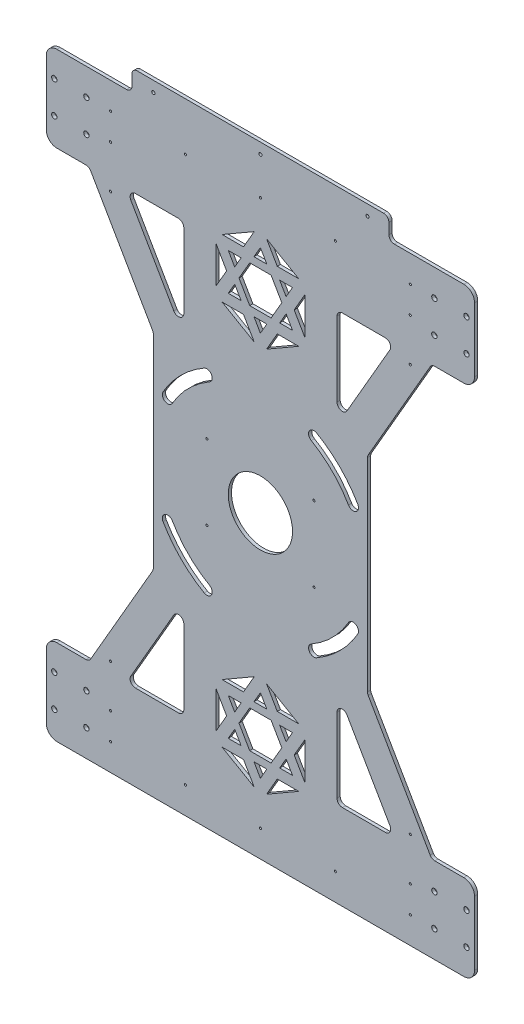
SolidWorks part; units mm, degrees
material "A-玻璃纤维"
ref_plane "前视基准面" through (0, 0, 0) normal (0, 0, 1) x (1, 0, 0)
ref_plane "上视基准面" through (0, 0, 0) normal (0, 1, 0) x (1, 0, 0)
ref_plane "右视基准面" through (0, 0, 0) normal (1, 0, 0) x (0, 0, -1)
other "Configuration Table"
sketch "草图2" plane through (0, 0, 0) normal (0, 0, 1) x (1, 0, 0)
  line L0 (-286.4774, 0) -> (382.3503, 0) construction
  line L1 (0, 257.3731) -> (0, 0) construction
  line L2 (-190, 280) -> (-125, 280)
  line L3 (200, 270) -> (200, 210)
  line L4 (190, 200) -> (162.8868, 200)
  line L5 (100, 94.7372) -> (100, -94.7372)
  line L6 (-100, 94.7372) -> (-100, -94.7372)
  line L7 (-190, 200) -> (-162.8868, 200)
  line L8 (-200, 270) -> (-200, 210)
  line L9 (-200, -270) -> (-200, -210)
  line L10 (-190, -200) -> (-162.8868, -200)
  line L11 (190, -200) -> (162.8868, -200)
  line L12 (200, -270) -> (200, -210)
  line L13 (-190, -280) -> (190, -280)
  line L14 (-120, 285) -> (-120, 295)
  line L15 (-115, 300) -> (115, 300)
  line L16 (120, 285) -> (120, 295)
  line L17 (125, 280) -> (190, 280)
  line L18 (100.6699, 97.2372) -> (158.5566, 197.5)
  line L19 (100.6699, -97.2372) -> (158.5566, -197.5)
  line L20 (-100.6699, -97.2372) -> (-158.5566, -197.5)
  line L21 (-100.6699, 97.2372) -> (-158.5566, 197.5)
  line L22 (0, -280) -> (0, -355.5287) construction
  arc A1 (200, 210) -> (190, 200) centre (190, 210) cw
  arc A2 (190, 280) -> (200, 270) centre (190, 270) cw
  arc A3 (-190, 280) -> (-200, 270) centre (-190, 270) ccw
  arc A4 (-200, 210) -> (-190, 200) centre (-190, 210) ccw
  arc A7 (-200, -210) -> (-190, -200) centre (-190, -210) cw
  arc A8 (-190, -280) -> (-200, -270) centre (-190, -270) cw
  arc A9 (190, -280) -> (200, -270) centre (190, -270) ccw
  arc A10 (200, -210) -> (190, -200) centre (190, -210) ccw
  arc A12 (120, 295) -> (115, 300) centre (115, 295) ccw
  arc A13 (-120, 295) -> (-115, 300) centre (-115, 295) cw
  arc A14 (120, 285) -> (125, 280) centre (125, 285) ccw
  arc A15 (-120, 285) -> (-125, 280) centre (-125, 285) cw
  arc A16 (158.5566, -197.5) -> (162.8868, -200) centre (162.8868, -195) ccw
  arc A17 (158.5566, 197.5) -> (162.8868, 200) centre (162.8868, 195) cw
  arc A18 (100.6699, 97.2372) -> (100, 94.7372) centre (105, 94.7372) ccw
  arc A19 (100.6699, -97.2372) -> (100, -94.7372) centre (105, -94.7372) cw
  arc A20 (-158.5566, -197.5) -> (-162.8868, -200) centre (-162.8868, -195) cw
  arc A21 (-100.6699, -97.2372) -> (-100, -94.7372) centre (-105, -94.7372) ccw
  arc A22 (-100.6699, 97.2372) -> (-100, 94.7372) centre (-105, 94.7372) cw
  arc A23 (-158.5566, 197.5) -> (-162.8868, 200) centre (-162.8868, 195) ccw
  point P5 (-200, 280)
  point P10 (-100, -200)
  point P12 (100, 200)
  point P15 (200, 200)
  point P18 (200, 280)
  point P26 (120, 280)
  point P28 (100, 0)
  point P29 (0, 280)
  point P30 (-200, 200)
  point P31 (-100, 200)
  point P47 (-120, 280)
  point P50 (-100, 0)
  point P51 (-200, -200)
  point P52 (0, -280)
  point P53 (200, -280)
  point P54 (200, -200)
  point P55 (100, -200)
  point P56 (-200, -280)
  point P61 (0, 300)
  point P64 (120, 300)
  point P67 (-120, 300)
  point P70 (160, -200)
  point P77 (160, 200)
  point P80 (100, 96.077)
  point P83 (100, -96.077)
  point P86 (-160, -200)
  point P89 (-100, -96.077)
  point P92 (-100, 96.077)
  point P95 (-160, 200)
  dimension "D5" = 5
  dimension "D8" = 5
  dimension "D11" = 5
  dimension "D1" = 400
  dimension "D2" = 80
  dimension "D3" = 100
  dimension "D4" = 560
  dimension "D6" = 120
  dimension "D7" = 20
  dimension "D9" = 30
  dimension "D10" = 120
extrude "凸台-拉伸1" add sketch "草图2" along normal blind 3
sketch "草图3" plane through (0, 0, 3) normal (0, 0, 1) x (1, 0, 0)
  line L0 (-216.9525, -240) -> (342.3439, -240) construction
  line L1 (-162.5, -255) -> (-162.5, -225) construction
  line L2 (-162.5, -225) -> (-192.5, -225) construction
  line L3 (-192.5, -225) -> (-192.5, -255) construction
  line L4 (-192.5, -255) -> (-162.5, -255) construction
  line L6 (-200, -210) -> (-200, -270) construction
  line L7 (-228.6627, 0) -> (0, 0) construction
  line L8 (0, 0) -> (0, 177.0482) construction
  circle A0 centre (-177.5, -240) radius 15 construction
  circle A1 centre (-162.5, -225) radius 2.5
  circle A2 centre (-192.5, -225) radius 2.5
  circle A3 centre (-192.5, -255) radius 2.5
  circle A4 centre (-162.5, -255) radius 2.5
  circle A5 centre (-162.5, 255) radius 2.5
  circle A6 centre (-192.5, 255) radius 2.5
  circle A7 centre (-192.5, 225) radius 2.5
  circle A8 centre (-162.5, 225) radius 2.5
  circle A9 centre (192.5, -255) radius 2.5
  circle A10 centre (192.5, -225) radius 2.5
  circle A11 centre (162.5, -225) radius 2.5
  circle A12 centre (162.5, -255) radius 2.5
  circle A13 centre (162.5, 225) radius 2.5
  circle A14 centre (192.5, 225) radius 2.5
  circle A15 centre (192.5, 255) radius 2.5
  circle A16 centre (162.5, 255) radius 2.5
  dimension "D3" = 5
  dimension "D1" = 30
  dimension "D2" = 7.5
extrude "切除-拉伸1" cut sketch "草图3" against normal blind 3
sketch "草图5" plane through (0, 0, 3) normal (0, 0, 1) x (1, 0, 0)
  line L0 (-120, 295) -> (-120, 285) construction
  line L1 (115, 300) -> (-115, 300) construction
  line L2 (120, 285) -> (120, 295) construction
  circle A0 centre (0, 290) radius 1.5
  circle A1 centre (100, 290) radius 1.5
  circle A2 centre (-100, 290) radius 1.5
  dimension "D1" = 3
  dimension "D2" = 3
  dimension "D3" = 3
  dimension "D6" = 20
  dimension "D4" = 20
  dimension "D5" = 10
extrude "切除-拉伸2" cut sketch "草图5" against normal blind 3
sketch "草图8" plane through (0, 0, 3) normal (0, 0, 1) x (1, 0, 0)
  line L0 (115, 300) -> (-115, 300) construction
  line L1 (20, 180) -> (10, 197.3205)
  line L2 (10, 197.3205) -> (-10, 197.3205)
  line L3 (-10, 197.3205) -> (-20, 180)
  line L4 (-20, 180) -> (-10, 162.6795)
  line L5 (-10, 162.6795) -> (10, 162.6795)
  line L6 (10, 162.6795) -> (20, 180)
  line L10 (13.9549, 162.6795) -> (42.8311, 162.6795) construction
  line L11 (20, 180) -> (33.9137, 155.9008) construction
  line L12 (24, 173.0718) -> (30, 162.6795)
  line L13 (30, 162.6795) -> (18, 162.6795)
  line L14 (18, 162.6795) -> (24, 173.0718)
  line L15 (-39.0474, 180) -> (64.6346, 180) construction
  line L16 (18, 197.3205) -> (24, 186.9282)
  line L17 (24, 186.9282) -> (30, 197.3205)
  line L18 (30, 197.3205) -> (18, 197.3205)
  line L19 (10, 197.3205) -> (-10, 162.6795) construction
  line L20 (0, 214.641) -> (6, 204.2487)
  line L21 (-6, 204.2487) -> (0, 214.641)
  line L22 (6, 204.2487) -> (-6, 204.2487)
  line L23 (-10, 197.3205) -> (10, 162.6795) construction
  line L24 (0, 145.359) -> (6, 155.7513)
  line L25 (6, 155.7513) -> (-6, 155.7513)
  line L26 (-6, 155.7513) -> (0, 145.359)
  line L27 (-24, 186.9282) -> (-18, 197.3205)
  line L28 (-18, 197.3205) -> (-30, 197.3205)
  line L29 (-30, 197.3205) -> (-24, 186.9282)
  line L30 (-30, 162.6795) -> (-24, 173.0718)
  line L31 (-18, 162.6795) -> (-30, 162.6795)
  line L32 (-24, 173.0718) -> (-18, 162.6795)
  line L33 (-2.8278, 219.5388) -> (10, 197.3205) construction
  line L34 (10, 197.3205) -> (34.5788, 197.3205) construction
  line L35 (5.7735, 224.641) -> (15.7735, 207.3205)
  line L36 (15.7735, 207.3205) -> (35.7735, 207.3205)
  line L37 (35.7735, 207.3205) -> (5.7735, 224.641)
  line L38 (-30, 162.6795) -> (30, 197.3205) construction
  line L39 (0, 214.641) -> (0, 130.8111) construction
  line L40 (-30, 197.3205) -> (30, 162.6795) construction
  line L41 (41.547, 197.3205) -> (41.547, 162.6795)
  line L42 (31.547, 180) -> (41.547, 197.3205)
  line L43 (41.547, 162.6795) -> (31.547, 180)
  line L44 (-41.547, 162.6795) -> (-41.547, 197.3205)
  line L45 (-31.547, 180) -> (-41.547, 162.6795)
  line L46 (-41.547, 197.3205) -> (-31.547, 180)
  line L47 (-5.7735, 135.359) -> (-15.7735, 152.6795)
  line L48 (-15.7735, 152.6795) -> (-35.7735, 152.6795)
  line L49 (-35.7735, 152.6795) -> (-5.7735, 135.359)
  line L50 (35.7735, 152.6795) -> (5.7735, 135.359)
  line L51 (15.7735, 152.6795) -> (35.7735, 152.6795)
  line L52 (5.7735, 135.359) -> (15.7735, 152.6795)
  line L53 (-35.7735, 207.3205) -> (-5.7735, 224.641)
  line L54 (-15.7735, 207.3205) -> (-35.7735, 207.3205)
  line L55 (-5.7735, 224.641) -> (-15.7735, 207.3205)
  line L56 (-132.25, 0) -> (191.392, 0) construction
  line L57 (-30, -197.3205) -> (30, -162.6795) construction
  line L58 (0, -214.641) -> (0, -130.8111) construction
  line L59 (-30, -162.6795) -> (30, -197.3205) construction
  line L60 (10, -197.3205) -> (34.5788, -197.3205) construction
  line L61 (-2.8278, -219.5388) -> (10, -197.3205) construction
  line L62 (-10, -197.3205) -> (10, -162.6795) construction
  line L63 (10, -197.3205) -> (-10, -162.6795) construction
  line L64 (-39.0474, -180) -> (64.6346, -180) construction
  line L65 (20, -180) -> (33.9137, -155.9008) construction
  line L66 (13.9549, -162.6795) -> (42.8311, -162.6795) construction
  line L67 (-5.7735, -224.641) -> (-15.7735, -207.3205)
  line L68 (-15.7735, -207.3205) -> (-35.7735, -207.3205)
  line L69 (-35.7735, -207.3205) -> (-5.7735, -224.641)
  line L70 (5.7735, -135.359) -> (15.7735, -152.6795)
  line L71 (15.7735, -152.6795) -> (35.7735, -152.6795)
  line L72 (35.7735, -152.6795) -> (5.7735, -135.359)
  line L73 (-35.7735, -152.6795) -> (-5.7735, -135.359)
  line L74 (-15.7735, -152.6795) -> (-35.7735, -152.6795)
  line L75 (-5.7735, -135.359) -> (-15.7735, -152.6795)
  line L76 (-41.547, -197.3205) -> (-31.547, -180)
  line L77 (-31.547, -180) -> (-41.547, -162.6795)
  line L78 (-41.547, -162.6795) -> (-41.547, -197.3205)
  line L79 (41.547, -162.6795) -> (31.547, -180)
  line L80 (31.547, -180) -> (41.547, -197.3205)
  line L81 (41.547, -197.3205) -> (41.547, -162.6795)
  line L82 (35.7735, -207.3205) -> (5.7735, -224.641)
  line L83 (15.7735, -207.3205) -> (35.7735, -207.3205)
  line L84 (5.7735, -224.641) -> (15.7735, -207.3205)
  line L85 (-24, -173.0718) -> (-18, -162.6795)
  line L86 (-18, -162.6795) -> (-30, -162.6795)
  line L87 (-30, -162.6795) -> (-24, -173.0718)
  line L88 (-30, -197.3205) -> (-24, -186.9282)
  line L89 (-18, -197.3205) -> (-30, -197.3205)
  line L90 (-24, -186.9282) -> (-18, -197.3205)
  line L91 (-6, -155.7513) -> (0, -145.359)
  line L92 (6, -155.7513) -> (-6, -155.7513)
  line L93 (0, -145.359) -> (6, -155.7513)
  line L94 (6, -204.2487) -> (-6, -204.2487)
  line L95 (-6, -204.2487) -> (0, -214.641)
  line L96 (0, -214.641) -> (6, -204.2487)
  line L97 (30, -197.3205) -> (18, -197.3205)
  line L98 (24, -186.9282) -> (30, -197.3205)
  line L99 (18, -197.3205) -> (24, -186.9282)
  line L100 (18, -162.6795) -> (24, -173.0718)
  line L101 (30, -162.6795) -> (18, -162.6795)
  line L102 (24, -173.0718) -> (30, -162.6795)
  line L103 (10, -162.6795) -> (20, -180)
  line L104 (-10, -162.6795) -> (10, -162.6795)
  line L105 (-20, -180) -> (-10, -162.6795)
  line L106 (-10, -197.3205) -> (-20, -180)
  line L107 (10, -197.3205) -> (-10, -197.3205)
  line L108 (20, -180) -> (10, -197.3205)
  circle A0 centre (0, 180) radius 17.3205 construction
  circle A1 centre (0, -180) radius 17.3205 construction
  dimension "D1" = 20
  dimension "D2" = 120
  dimension "D3" = 8
  dimension "D4" = 10
  dimension "D5" = 10
  dimension "D6" = 20
extrude "切除-拉伸3" cut sketch "草图8" against normal blind 3
sketch "草图9" plane through (0, 0, 3) normal (0, 0, 1) x (1, 0, 0)
  line L0 (-190, 200) -> (242.0399, 200) construction
  line L1 (71.547, 195) -> (71.547, 125.4552)
  line L2 (80.8771, 122.9552) -> (121.0289, 192.5)
  line L3 (116.6987, 200) -> (76.547, 200)
  line L4 (-66.849, 0) -> (0, 0) construction
  line L5 (0, 0) -> (0, 96.077) construction
  line L6 (41.547, 162.6795) -> (41.547, 197.3205) construction
  line L7 (100.6699, 97.2372) -> (158.5566, 197.5) construction
  line L8 (-116.6987, 200) -> (-76.547, 200)
  line L9 (-80.8771, 122.9552) -> (-121.0289, 192.5)
  line L10 (-71.547, 195) -> (-71.547, 125.4552)
  line L11 (-71.547, -195) -> (-71.547, -125.4552)
  line L12 (-80.8771, -122.9552) -> (-121.0289, -192.5)
  line L13 (-116.6987, -200) -> (-76.547, -200)
  line L14 (116.6987, -200) -> (76.547, -200)
  line L15 (80.8771, -122.9552) -> (121.0289, -192.5)
  line L16 (71.547, -195) -> (71.547, -125.4552)
  arc A0 (80.8771, -122.9552) -> (71.547, -125.4552) centre (76.547, -125.4552) ccw
  arc A1 (76.547, -200) -> (71.547, -195) centre (76.547, -195) cw
  arc A2 (116.6987, -200) -> (121.0289, -192.5) centre (116.6987, -195) ccw
  arc A3 (-121.0289, -192.5) -> (-116.6987, -200) centre (-116.6987, -195) ccw
  arc A4 (-71.547, -125.4552) -> (-80.8771, -122.9552) centre (-76.547, -125.4552) ccw
  arc A5 (-71.547, -195) -> (-76.547, -200) centre (-76.547, -195) cw
  arc A6 (71.547, 125.4552) -> (80.8771, 122.9552) centre (76.547, 125.4552) ccw
  arc A7 (121.0289, 192.5) -> (116.6987, 200) centre (116.6987, 195) ccw
  arc A8 (71.547, 195) -> (76.547, 200) centre (76.547, 195) cw
  arc A9 (-80.8771, 122.9552) -> (-71.547, 125.4552) centre (-76.547, 125.4552) ccw
  arc A10 (-76.547, 200) -> (-71.547, 195) centre (-76.547, 195) cw
  arc A11 (-116.6987, 200) -> (-121.0289, 192.5) centre (-116.6987, 195) ccw
  point P25 (71.547, -106.7949)
  point P28 (71.547, -200)
  point P31 (125.359, -200)
  point P34 (-125.359, -200)
  point P37 (-71.547, -106.7949)
  point P40 (-71.547, -200)
  point P43 (71.547, 106.7949)
  point P46 (125.359, 200)
  point P49 (71.547, 200)
  point P52 (-71.547, 106.7949)
  point P55 (-71.547, 200)
  point P58 (-125.359, 200)
  dimension "D3" = 5
  dimension "D1" = 30
  dimension "D2" = 30
extrude "切除-拉伸4" cut sketch "草图9" against normal blind 10
sketch "草图11" plane through (0, 0, 3) normal (0, 0, 1) x (1, 0, 0)
  line L0 (-200, -210) -> (-200, -270) construction
  line L1 (-190, -280) -> (190, -280) construction
  circle A0 centre (-120, -265) radius 1
  circle A1 centre (-80, -265) radius 1
  circle A2 centre (-40, -265) radius 1
  circle A3 centre (0, -265) radius 1
  circle A4 centre (40, -265) radius 1
  circle A5 centre (80, -265) radius 1
  circle A6 centre (120, -265) radius 1
  dimension "D1" = 2
  dimension "D3" = 15
  dimension "D2" = 80
  dimension "D4" = 7
sketch "草图13" plane through (0, 0, 3) normal (0, 0, 1) x (1, 0, 0)
  line L1 (115, 300) -> (-115, 300) construction
  line L2 (0, 64.205) -> (0, 0) construction
  line L3 (0, 0) -> (63.4246, 0) construction
  circle A0 centre (0, 255) radius 1
  circle A2 centre (70, 255) radius 1
  circle A3 centre (140, 255) radius 1
  circle A4 centre (-140, 255) radius 1
  circle A5 centre (-70, 255) radius 1
  circle A6 centre (-70, -255) radius 1
  circle A7 centre (-140, -255) radius 1
  circle A8 centre (140, -255) radius 1
  circle A9 centre (70, -255) radius 1
  circle A10 centre (0, -255) radius 1
  point P12 (150.5477, 255)
  point P13 (0, 0)
  dimension "D1" = 2
  dimension "D4" = 70
  dimension "D2" = 45
  dimension "D3" = 3
extrude "切除-拉伸6" cut sketch "草图13" against normal blind 10
sketch "草图14" plane through (0, 0, 3) normal (0, 0, 1) x (1, 0, 0)
  circle A0 centre (0, 0) radius 30
  dimension "D1" = 60
extrude "切除-拉伸7" cut sketch "草图14" against normal blind 10
sketch "草图15" plane through (0, 0, 3) normal (0, 0, 1) x (1, 0, 0)
  line L0 (-125, 280) -> (-190, 280) construction
  line L3 (-200, 270) -> (-200, 210) construction
  line L5 (-79.0544, 0) -> (0, 0) construction
  line L6 (0, 0) -> (0, 90.0166) construction
  circle A3 centre (-140, 230) radius 1
  circle A4 centre (-140, 190) radius 1
  circle A7 centre (140, 190) radius 1
  circle A8 centre (140, 230) radius 1
  circle A9 centre (140, -230) radius 1
  circle A10 centre (140, -190) radius 1
  circle A11 centre (-140, -190) radius 1
  circle A12 centre (-140, -230) radius 1
  dimension "D2" = 60
  dimension "D4" = 2
  dimension "D8" = 40
  dimension "D1" = 50
  dimension "D7" = 2
extrude "切除-拉伸8" cut sketch "草图15" against normal blind 10
sketch "草图20" plane through (0, 0, 3) normal (0, 0, 1) x (1, 0, 0)
  line L1 (-50, 35) -> (50, 35) construction
  line L2 (-50, 35) -> (-50, -35) construction
  line L3 (-50, -35) -> (50, -35) construction
  line L4 (50, 35) -> (50, -35) construction
  line L5 (-50, 35) -> (50, -35) construction
  line L6 (-50, -35) -> (50, 35) construction
  circle A0 centre (-50, 35) radius 1
  circle A1 centre (-50, -35) radius 1
  circle A2 centre (50, -35) radius 1
  circle A3 centre (50, 35) radius 1
  point P0 (0, 0)
  dimension "D3" = 2
  dimension "D4" = 2
  dimension "D5" = 2
  dimension "D6" = 2
  dimension "D1" = 100
  dimension "D2" = 70
extrude "切除-拉伸10" cut sketch "草图20" against normal blind 10
sketch "草图22" plane through (0, 0, 3) normal (0, 0, 1) x (1, 0, 0)
  line L0 (0, 120.825) -> (0, 0) construction
  line L1 (0, 0) -> (70.7107, 70.7107) construction
  line L2 (50, 86.6025) -> (0, 0) construction
  line L3 (0, 0) -> (86.6025, 50) construction
  circle A0 centre (0, 0) radius 100 construction
  arc A1 (50, 86.6025) -> (86.6025, 50) centre (0, 0) cw construction
  arc A2 (90.9327, 52.5) -> (52.5, 90.9327) centre (0, 0) ccw
  arc A3 (82.2724, 47.5) -> (47.5, 82.2724) centre (0, 0) ccw
  arc A4 (82.2724, 47.5) -> (90.9327, 52.5) centre (86.6025, 50) ccw
  arc A5 (52.5, 90.9327) -> (47.5, 82.2724) centre (50, 86.6025) ccw
  arc A6 (47.5, -82.2724) -> (82.2724, -47.5) centre (0, 0) ccw
  arc A7 (47.5, -82.2724) -> (52.5, -90.9327) centre (50, -86.6025) ccw
  arc A8 (90.9327, -52.5) -> (82.2724, -47.5) centre (86.6025, -50) ccw
  arc A9 (52.5, -90.9327) -> (90.9327, -52.5) centre (0, 0) ccw
  arc A10 (86.6025, -50) -> (50, -86.6025) centre (0, 0) cw construction
  arc A11 (-82.2724, -47.5) -> (-47.5, -82.2724) centre (0, 0) ccw
  arc A12 (-82.2724, -47.5) -> (-90.9327, -52.5) centre (-86.6025, -50) ccw
  arc A13 (-52.5, -90.9327) -> (-47.5, -82.2724) centre (-50, -86.6025) ccw
  arc A14 (-90.9327, -52.5) -> (-52.5, -90.9327) centre (0, 0) ccw
  arc A15 (-50, -86.6025) -> (-86.6025, -50) centre (0, 0) cw construction
  arc A16 (-47.5, 82.2724) -> (-82.2724, 47.5) centre (0, 0) ccw
  arc A17 (-47.5, 82.2724) -> (-52.5, 90.9327) centre (-50, 86.6025) ccw
  arc A18 (-90.9327, 52.5) -> (-82.2724, 47.5) centre (-86.6025, 50) ccw
  arc A19 (-52.5, 90.9327) -> (-90.9327, 52.5) centre (0, 0) ccw
  arc A20 (-86.6025, 50) -> (-50, 86.6025) centre (0, 0) cw construction
  point P6 (70.7107, 70.7107)
  point P18 (70.7107, -70.7107)
  point P25 (-70.7107, -70.7107)
  point P32 (-70.7107, 70.7107)
  point P37 (0, 0)
  dimension "D1" = 200
  dimension "D3" = 5
  dimension "D2" = 45
  dimension "D5" = 30
  dimension "D4" = 4
extrude "切除-拉伸11" cut sketch "草图22" against normal blind 3
